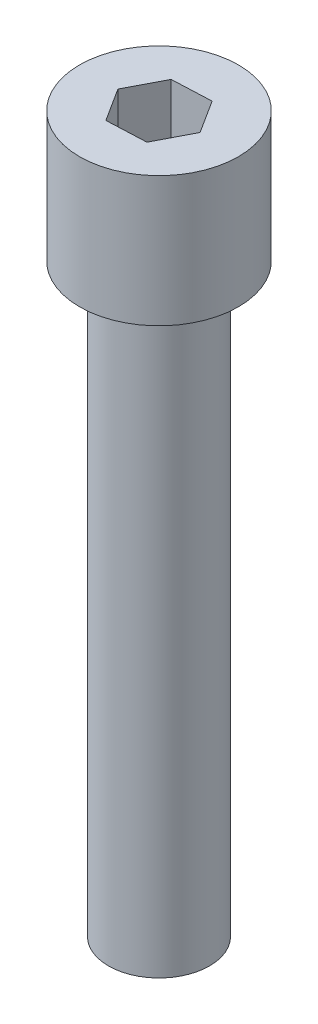
SolidWorks part; units mm, degrees
material "Aço carbono simples"
ref_plane "Plano frontal" through (0, 0, 0) normal (0, 0, 1) x (1, 0, 0)
ref_plane "Plano superior" through (0, 0, 0) normal (0, 1, 0) x (1, 0, 0)
ref_plane "Plano direito" through (0, 0, 0) normal (1, 0, 0) x (0, 0, -1)
sketch "Esboço1" plane through (0, 0, 0) normal (0, 1, 0) x (1, 0, 0)
  circle A0 centre (0, 0) radius 3.5
  dimension "D1" = 7
extrude "Ressalto-extrusão1" add sketch "Esboço1" along normal blind 40.5
sketch "Esboço2" plane through (0, 40.5, 0) normal (0, 1, 0) x (1, 0, 0)
  circle A0 centre (0, 0) radius 5.5
  dimension "D1" = 11
extrude "Ressalto-extrusão2" add sketch "Esboço2" along normal blind 9
sketch "Esboço3" plane through (0, 49.5, 0) normal (0, 1, 0) x (1, 0, 0)
  line L1 (1.2585, 2.4179) -> (-1.4647, 2.2989)
  line L2 (-1.4647, 2.2989) -> (-2.7232, -0.119)
  line L3 (-2.7232, -0.119) -> (-1.2585, -2.4179)
  line L4 (-1.2585, -2.4179) -> (1.4647, -2.2989)
  line L5 (1.4647, -2.2989) -> (2.7232, 0.119)
  line L6 (2.7232, 0.119) -> (1.2585, 2.4179)
  circle A0 centre (0, 0) radius 2.3606 construction
extrude "Corte-extrusão1" cut sketch "Esboço3" against normal blind 5
